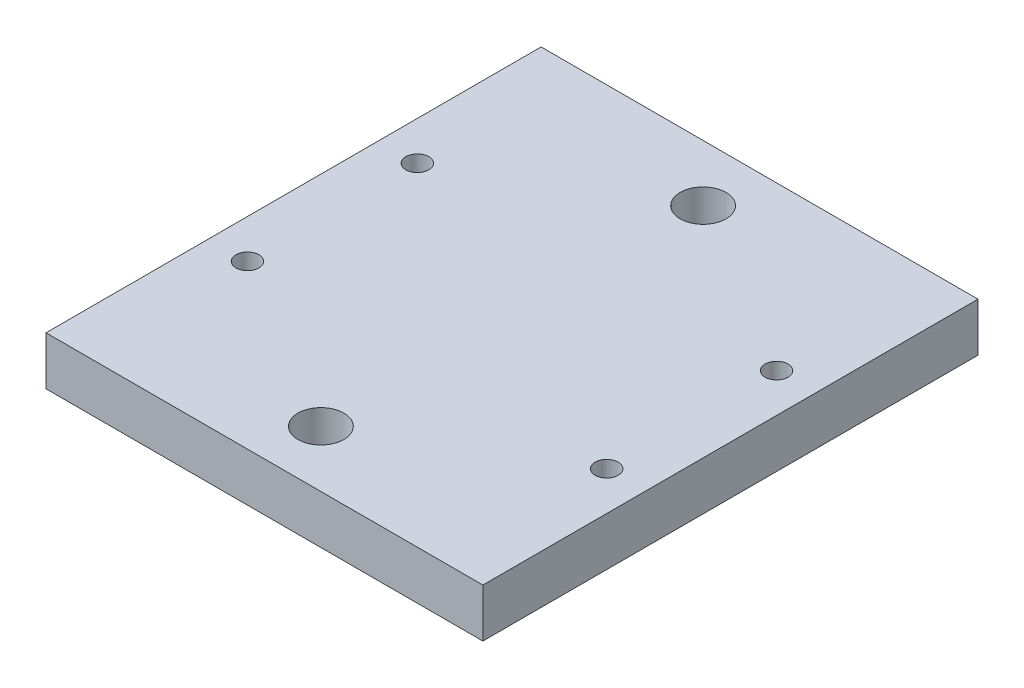
SolidWorks part; units mm, degrees
ref_plane "Front Plane" through (0, 0, 0) normal (0, 0, 1) x (1, 0, 0)
ref_plane "Top Plane" through (0, 0, 0) normal (0, 1, 0) x (1, 0, 0)
ref_plane "Right Plane" through (0, 0, 0) normal (1, 0, 0) x (0, 0, -1)
sketch "Sketch1" plane through (0, 0, 0) normal (0, 1, 0) x (1, 0, 0)
  line L0 (28.575, 57.385) -> (28.575, 7.385) construction
  line L1 (0, 0) -> (57.15, 0)
  line L2 (0, 0) -> (0, 64.77)
  line L3 (0, 64.77) -> (57.15, 64.77)
  line L4 (57.15, 0) -> (57.15, 64.77)
  line L5 (5.08, 43.4975) -> (52.07, 43.4975) construction
  line L6 (5.08, 43.4975) -> (5.08, 21.2725) construction
  circle A0 centre (28.575, 57.385) radius 3
  circle A1 centre (28.575, 7.385) radius 3
  circle A2 centre (52.07, 43.4975) radius 1.5
  circle A3 centre (52.07, 21.2725) radius 1.5
  circle A4 centre (5.08, 43.4975) radius 1.5
  circle A5 centre (5.08, 21.2725) radius 1.5
  point P17 (28.575, 32.385)
  point P18 (57.15, 32.385)
  point P19 (28.575, 43.4975)
  point P20 (5.08, 32.385)
  point P21 (0, 32.385)
  point P23 (28.575, 0)
  dimension "D4" = 6
  dimension "D5" = 3
  dimension "D1" = 57.15
  dimension "D2" = 64.77
  dimension "D3" = 50
  dimension "D6" = 46.99
  dimension "D7" = 22.225
extrude "Boss-Extrude1" add sketch "Sketch1" along normal blind 6.35 contours L1 L4 L3 L2 A5 A4 A3 A2 A1 A0
